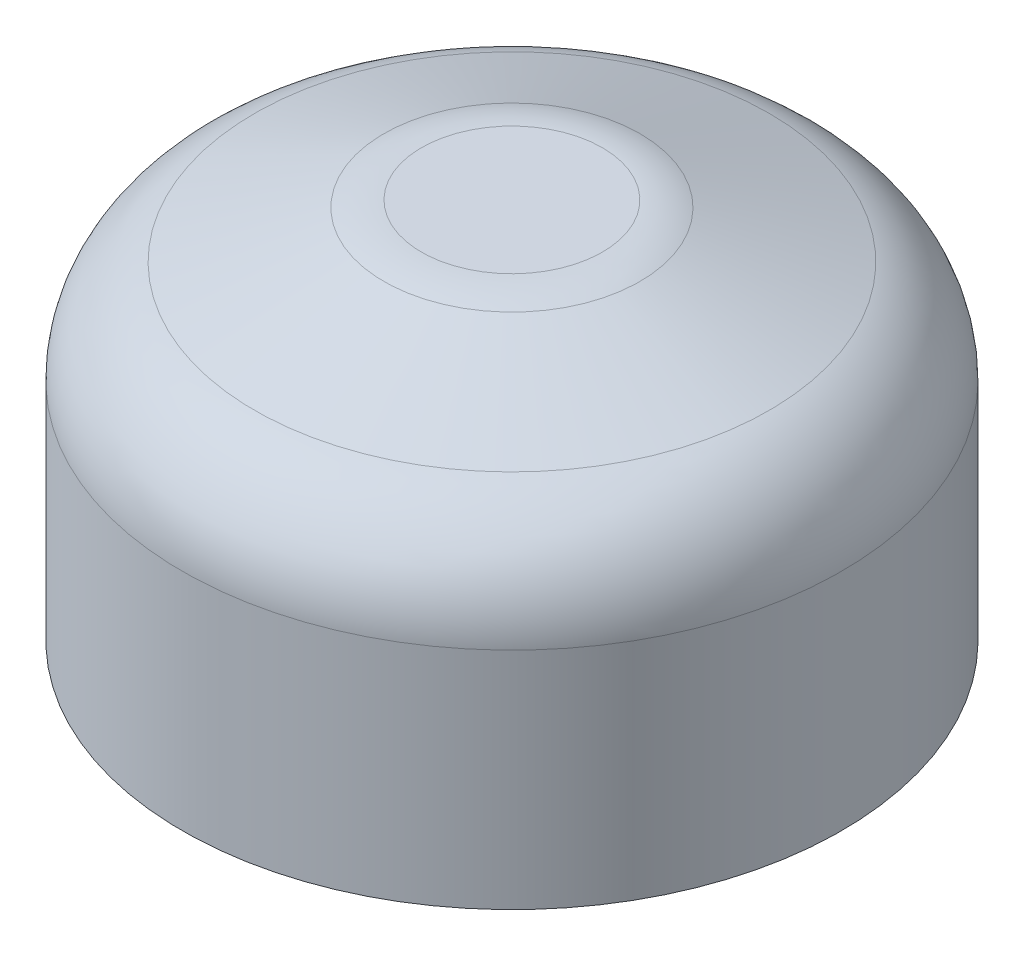
SolidWorks part; units mm, degrees
material "Delrin 2700 NC010, Low Viscosity Acetal Copolymer (SS)"
ref_plane "Front-Back Midplane" through (0, 0, 0) normal (0, 0, 1) x (1, 0, 0)
ref_plane "Horizontal Midplane" through (0, 0, 0) normal (0, 1, 0) x (1, 0, 0)
ref_plane "Left-Right Midplane" through (0, 0, 0) normal (1, 0, 0) x (0, 0, -1)
ref_axis "Axis1" through (0, -0.5514, 0) along (0, 1, 0)
sketch "Sketch1" plane through (0, 0, 0) normal (0, 0, 1) x (1, 0, 0)
  line L0 (-9.525, 6.4943) -> (-9.525, 0)
  line L1 (-9.525, 0) -> (0, 0)
  line L2 (0, 0) -> (0, 11.0287)
  line L3 (0, 11.0287) -> (-2.6152, 11.0287)
  line L4 (-7.4359, 9.4778) -> (-3.7011, 10.8372)
  arc A0 (-9.525, 6.4943) -> (-7.4359, 9.4778) centre (-6.35, 6.4943) cw
  arc A1 (-2.6152, 11.0287) -> (-3.7011, 10.8372) centre (-2.6152, 7.8537) ccw
  point P10 (-3.175, 11.0287)
  dimension "D3" = 20
  dimension "D5" = 3.175
  dimension "D1" = 11.0287
  dimension "D2" = 9.525
  dimension "D4" = 3.175
revolve "Revolve1" add sketch "Sketch1" angle 360 about axis through (0, -0.5514, 0) along (0, 1, 0)
hole_wizard "#4-40 Tapped Hole1" positions "Sketch3" profile "Sketch2" tap size "#4-40" standard "Ansi Inch"
sketch "Sketch3" plane through (0, 0, 0) normal (0, -1, 0) x (1, 0, 0)
  point P0 (0, 5.715)
  dimension "D1" = 5.715
sketch "Sketch2" plane through (0, 0, 5.715) normal (1, 0, 0) x (0, 0, -1)
  line L0 (0, 0) -> (0, 9.1882)
  line L1 (0, 9.1882) -> (1.1303, 8.509)
  line L2 (1.1303, 8.509) -> (1.1303, 0)
  line L5 (1.1303, 0) -> (0, 0)
  line L10 (0, 9.1882) -> (-1.1303, 8.509) construction
  line L11 (0, -6.35) -> (0, 107.95) construction
  dimension "Tap Drill Dia." = 2.2606
  dimension "Tap Drill Depth" = 8.509
  dimension "Drill Angle" = 118
cosmetic thread "Hole Thread1" parameters "D1"=6.604, "D2"=2.8448
pattern_circular "CirPattern1" count 3 over 360 about axis through (0, 0, 0) along (0, 1, 0) of "#4-40 Tapped Hole1"
